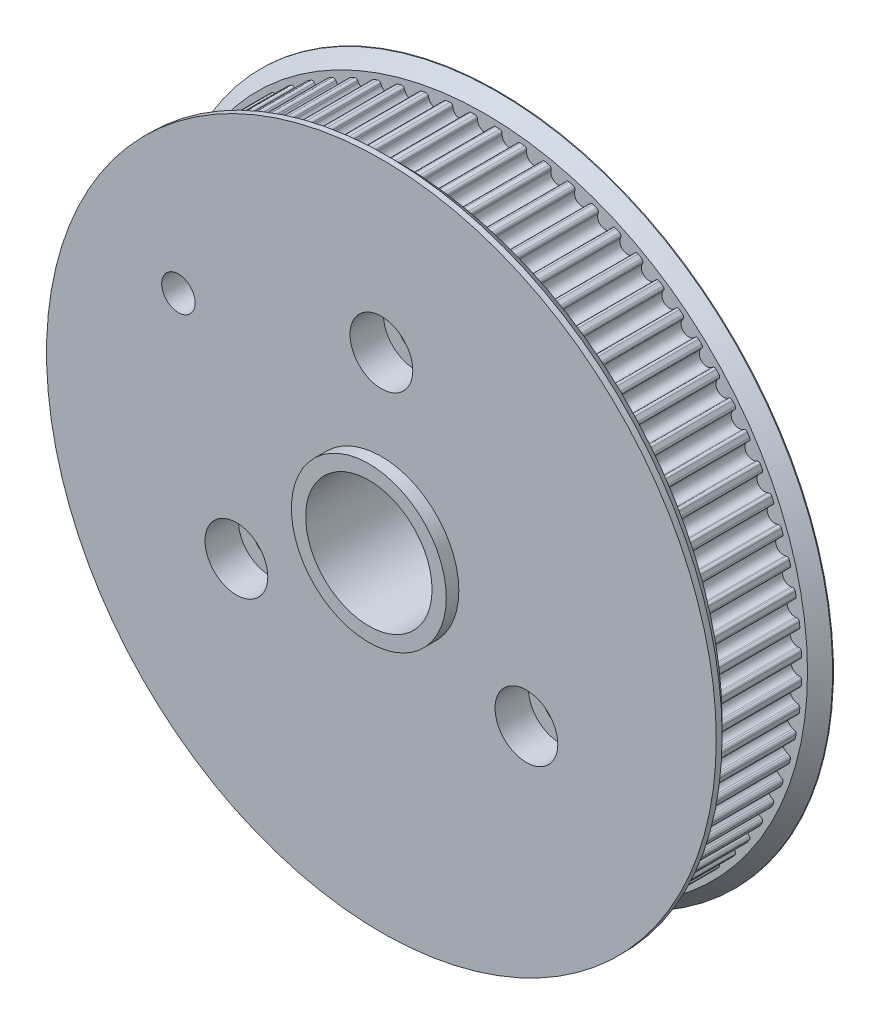
SolidWorks part; units mm, degrees
ref_plane "Front Plane" through (0, 0, 0) normal (0, 0, 1) x (1, 0, 0)
ref_plane "Top Plane" through (0, 0, 0) normal (0, 1, 0) x (1, 0, 0)
ref_plane "Right Plane" through (0, 0, 0) normal (1, 0, 0) x (0, 0, -1)
sketch "Sketch1" plane through (0, 0, 0) normal (0, 0, 1) x (1, 0, 0)
  circle A0 centre (0, 0) radius 37.815
  dimension "D1" = 75.63
extrude "Boss-Extrude1" add sketch "Sketch1" along normal blind 10.2
sketch "Sketch3" plane through (0, 0, 10.2) normal (0, 0, 1) x (1, 0, 0)
  line L0 (0, 37.815) -> (0, 0) construction
  line L1 (-0.9032, 37.3341) -> (-1.0564, 38.5817) construction
  line L2 (0.9032, 37.3341) -> (1.0576, 38.5912) construction
  line L3 (0, 0) -> (-1.4846, 37.7858) construction
  line L4 (0, 0) -> (1.4846, 37.7858) construction
  line L5 (-0.9275, 37.5315) -> (-0.9032, 37.3341)
  line L6 (0.9032, 37.3341) -> (0.9275, 37.5315)
  line L7 (-1.4846, 37.7858) -> (0, 42.815)
  line L8 (0, 42.815) -> (1.4846, 37.7858)
  circle A0 centre (0, 0) radius 37.815 construction
  arc A1 (-0.9032, 37.3341) -> (0.9032, 37.3341) centre (0, 37.445) ccw
  circle A2 centre (0, 0) radius 37.815 construction
  arc A3 (-0.9275, 37.5315) -> (-1.235, 37.7948) centre (-1.2252, 37.495) ccw
  arc A4 (0.9275, 37.5315) -> (1.235, 37.7948) centre (1.2252, 37.495) cw
  arc A5 (1.235, 37.7948) -> (1.4846, 37.7858) centre (0, 0) cw
  arc A6 (-1.235, 37.7948) -> (-1.4846, 37.7858) centre (0, 0) ccw
  dimension "D2" = 0.37
  dimension "D1" = 0.91
  dimension "D3" = 14
  dimension "D4" = 0.3
  dimension "D7" = 0.3
  dimension "D5" = 4.5
  dimension "D6" = 2.25
  dimension "D8" = 5
extrude "Cut-Extrude1" cut sketch "Sketch3" against normal up to surface (10.2 mm away) up to face at (37.815, 0, 0)
pattern_circular "CirPattern1" count 80 over 360 about axis through (0, 0, 0) along (0, 0, 1) of "Cut-Extrude1"
sketch "Sketch4" plane through (0, 0, 10.2) normal (0, 0, 1) x (1, 0, 0)
  circle A0 centre (0, 0) radius 40
  dimension "D1" = 80
extrude "Boss-Extrude2" add sketch "Sketch4" along normal blind 2.2
sketch "Sketch5" plane through (0, 0, 12.4) normal (0, 0, 1) x (1, 0, 0)
  circle A0 centre (0, 0) radius 7.55
  dimension "D1" = 15.1
extrude "Cut-Extrude2" cut sketch "Sketch5" against normal blind 24.6
chamfer "Chamfer1" distance 1.5 angle 45 1 edges at (40, 0, 10.2)
sketch "Sketch8" plane through (0, 0, 12.4) normal (0, 0, 1) x (1, 0, 0)
  line L1 (0, 0) -> (0, 20) construction
  circle A0 centre (0, 20) radius 2
  circle A7 centre (17.3205, -10) radius 2
  circle A8 centre (-17.3205, -10) radius 2
  point P9 (0, 0)
  point P15 (0, 0)
  dimension "D3" = 4
  dimension "D1" = 3
  dimension "D2" = 20
extrude "Cut-Extrude6" cut sketch "Sketch8" against normal up to surface (12.4 mm away) up to face at (7.55, 0, 0)
sketch "Sketch9" plane through (0, 0, 12.4) normal (0, 0, 1) x (1, 0, 0)
  circle A0 centre (0, 20) radius 3.75
  circle A1 centre (17.3205, -10) radius 3.75
  circle A2 centre (-17.3205, -10) radius 3.75
  dimension "D2" = 7.5
  dimension "D3" = 7.5
  dimension "D4" = 7.5
extrude "Cut-Extrude5" cut sketch "Sketch9" against normal blind 4
sketch "草图1" plane through (0, 0, 12.4) normal (0, 0, 1) x (1, 0, 0)
  circle A0 centre (0, 0) radius 9.25
  circle M5 centre (0, 0) radius 7.55
  dimension "D1" = 18.5
extrude "凸台-拉伸1" add sketch "草图1" along normal blind 1.5 contours A0 M5
sketch "草图2" plane through (0, 0, 0) normal (0, 0, -1) x (-1, 0, 0)
  circle A0 centre (0, 0) radius 40
  dimension "D1" = 80
extrude "凸台-拉伸2" add sketch "草图2" along normal blind 1.6
chamfer "倒角1" distance 1.5 angle 45 1 edges at (-40, 0, 0)
sketch "草图3" plane through (0, 0, -1.6) normal (0, 0, -1) x (-1, 0, 0)
  circle A0 centre (0, 0) radius 7.55
  dimension "D1" = 15.1
extrude "切除-拉伸1" cut sketch "草图3" against normal through all
sketch "草图4" plane through (0, 0, -1.6) normal (0, 0, -1) x (-1, 0, 0)
  circle A0 centre (-17.3205, -10) radius 2
  circle A1 centre (17.3205, -10) radius 2
  circle A2 centre (0, 20) radius 2
extrude "切除-拉伸2" cut sketch "草图4" against normal through all
sketch "草图5" plane through (0, 0, 12.4) normal (0, 0, 1) x (1, 0, 0)
  line L0 (0, 0) -> (0, -28) construction
  circle A0 centre (0, -28) radius 2
  dimension "D2" = 4
  dimension "D1" = 28
sketch "草图6" plane through (0, 0, 12.4) normal (0, 0, 1) x (1, 0, 0)
  circle A1 centre (-24.2487, 14) radius 2
  dimension "D1" = 4
extrude "切除-拉伸3" cut sketch "草图6" against normal blind 3
